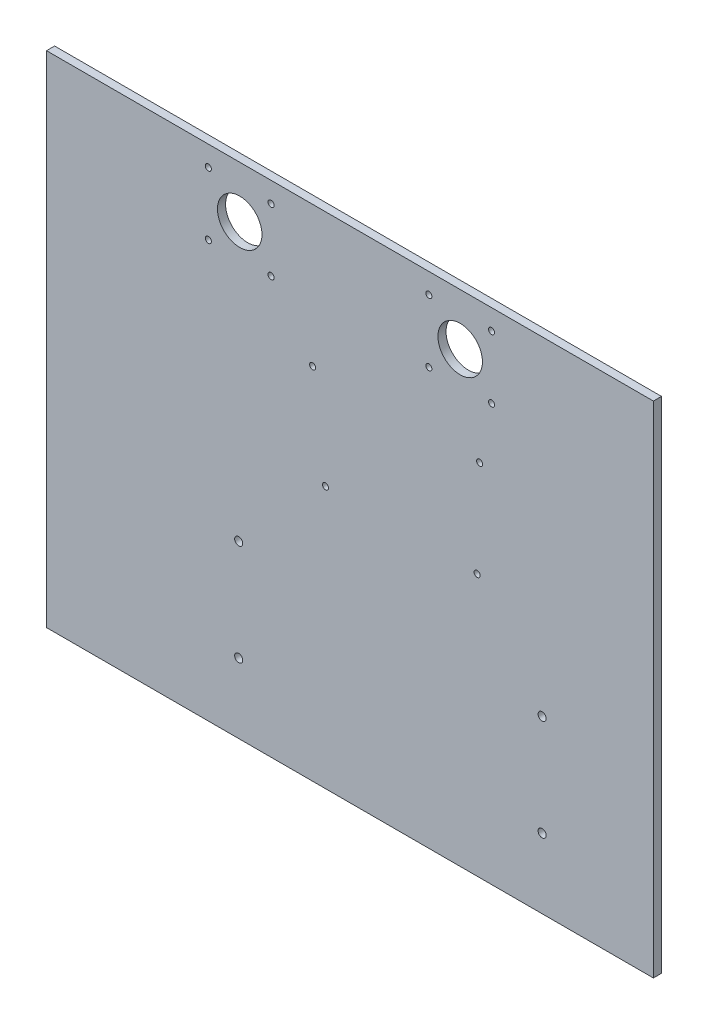
SolidWorks part; units mm, degrees
ref_plane "Front Plane" through (0, 0, 0) normal (0, 0, 1) x (1, 0, 0)
ref_plane "Top Plane" through (0, 0, 0) normal (0, 1, 0) x (1, 0, 0)
ref_plane "Right Plane" through (0, 0, 0) normal (1, 0, 0) x (0, 0, -1)
sketch "Sketch1" plane through (0, 0, 0) normal (0, 0, 1) x (1, 0, 0)
  line L0 (-39, 82.5) -> (-70, 82.5) construction
  line L1 (150, -123.5) -> (-150, -123.5)
  line L2 (150, -123.5) -> (150, 123.5)
  line L3 (150, 123.5) -> (-150, 123.5)
  line L4 (-150, -123.5) -> (-150, 123.5)
  line L5 (150, -123.5) -> (-150, 123.5) construction
  line L6 (150, 123.5) -> (-150, -123.5) construction
  line L7 (-39, 82.5) -> (-39, 113.5) construction
  line L8 (-39, 113.5) -> (-70, 113.5) construction
  line L9 (-70, 82.5) -> (-70, 113.5) construction
  line L10 (-39, 82.5) -> (-70, 113.5) construction
  line L11 (-39, 113.5) -> (-70, 82.5) construction
  line L12 (0, 123.5) -> (0, -133.2191) construction
  line L13 (39, 113.5) -> (70, 82.5) construction
  line L14 (39, 82.5) -> (70, 113.5) construction
  line L15 (70, 82.5) -> (70, 113.5) construction
  line L16 (39, 113.5) -> (70, 113.5) construction
  line L17 (39, 82.5) -> (39, 113.5) construction
  line L18 (39, 82.5) -> (70, 82.5) construction
  circle A0 centre (-70, 113.5) radius 1.5
  circle A1 centre (-39, 113.5) radius 1.5
  circle A2 centre (70, 82.5) radius 1.5
  circle A3 centre (-54.5, 98) radius 11
  circle A4 centre (-39, 82.5) radius 1.5
  circle A5 centre (-70, 82.5) radius 1.5
  circle A6 centre (39, 82.5) radius 1.5
  circle A7 centre (54.5, 98) radius 11
  circle A8 centre (39, 113.5) radius 1.5
  circle A9 centre (70, 113.5) radius 1.5
  circle A10 centre (95, -39) radius 2
  circle A11 centre (95, -89) radius 2
  circle A12 centre (-55, -39) radius 2
  circle A13 centre (-55, -89) radius 2
  circle A14 centre (64.1213, 54.1951) radius 1.5
  circle A16 centre (-12.0787, 5.9351) radius 1.5
  circle A17 centre (62.8513, 5.9351) radius 1.5
  circle A18 centre (-18.4287, 54.1951) radius 1.5
  point P0 (0, 0)
  dimension "D3" = 22
  dimension "D5" = 3
  dimension "D6" = 80
  dimension "D8" = 3
  dimension "D9" = 3
  dimension "D10" = 3
  dimension "D11" = 2
  dimension "D12" = 2
  dimension "D13" = 2
  dimension "D14" = 2
  dimension "D19" = 3
  dimension "D20" = 3
  dimension "D21" = 3
  dimension "D22" = 3
  dimension "D1" = 300
  dimension "D2" = 247
  dimension "D4" = 31
  dimension "D7" = 10
  dimension "D15" = 95
  dimension "D16" = 150
  dimension "D17" = 50
  dimension "D18" = 34.5
  dimension "D23" = 82.55
  dimension "D24" = 48.26
  dimension "D25" = 74.93
  dimension "D26" = 48.26
  dimension "D27" = 69.3049
  dimension "D28" = 85.8787
extrude "Boss-Extrude1" add sketch "Sketch1" along normal blind 4
